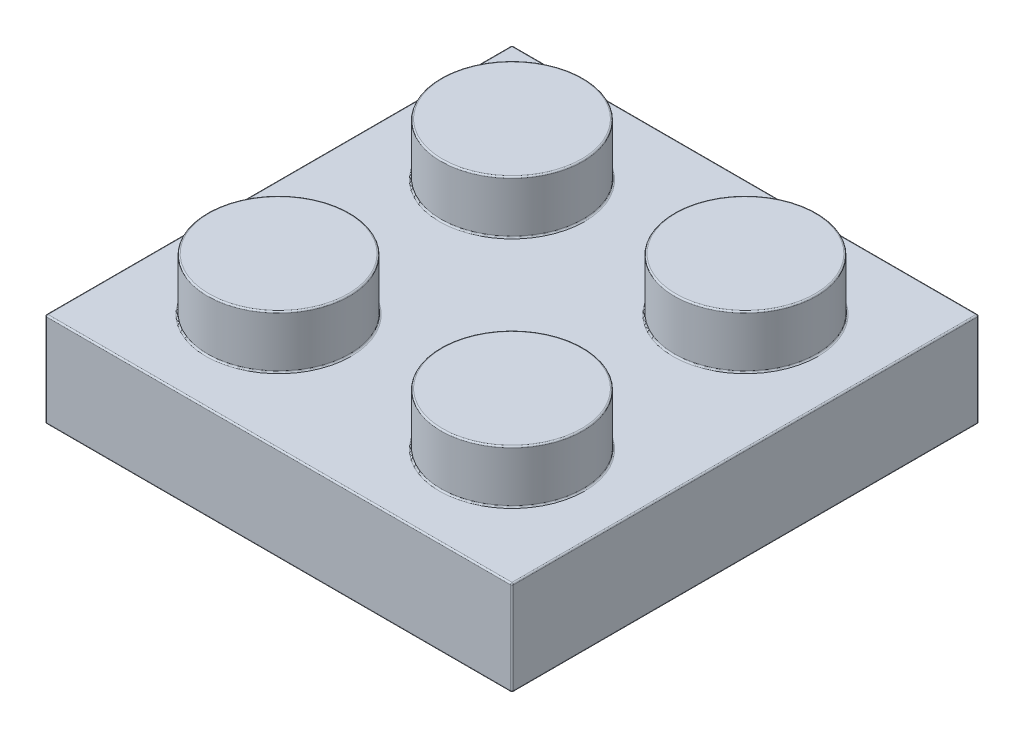
SolidWorks part; units mm, degrees
ref_plane "Front Plane" through (0, 0, 0) normal (0, 0, 1) x (1, 0, 0)
ref_plane "Top Plane" through (0, 0, 0) normal (0, 1, 0) x (1, 0, 0)
ref_plane "Right Plane" through (0, 0, 0) normal (1, 0, 0) x (0, 0, -1)
sketch "Sketch1" plane through (0, 0, 0) normal (0, 1, 0) x (1, 0, 0)
  line L1 (-3.98, 3.98) -> (3.98, 3.98)
  line L2 (-3.98, 3.98) -> (-3.98, -3.98)
  line L3 (-3.98, -3.98) -> (3.98, -3.98)
  line L4 (3.98, 3.98) -> (3.98, -3.98)
  line L5 (-3.98, 3.98) -> (3.98, -3.98) construction
  line L6 (-3.98, -3.98) -> (3.98, 3.98) construction
  point P0 (0, 0)
  dimension "D1" = 7.96
extrude "Extrude1" add sketch "Sketch1" along normal blind 3.22
sketch "Sketch2" plane through (0, 3.22, 0) normal (0, 1, 0) x (1, 0, 0)
  circle A0 centre (0, 0) radius 2.425
  dimension "D1" = 4.85
extrude "Extrude2" add sketch "Sketch2" along normal blind 1.8
pattern_linear "LPattern1" count 2 spacing 7.96 along (1, 0, 0) of "Extrude2", "Extrude1"
pattern_linear "LPattern2" count 2 spacing 7.96 along (0, 0, -1) of "LPattern1", "Extrude1", "Extrude2"
shell "Shell1" thickness 1.55
sketch "Sketch3" plane through (0, 1.67, 0) normal (0, -1, 0) x (1, 0, 0)
  line L0 (10.39, -10.39) -> (-2.43, -10.39) construction
  line L1 (-2.43, -10.39) -> (-2.43, 2.43) construction
  line L2 (-2.43, 2.43) -> (10.39, 2.43) construction
  line L3 (10.39, 2.43) -> (10.39, -10.39) construction
  line L4 (10.39, -10.39) -> (-2.43, -10.39)
  line L5 (-2.43, -10.39) -> (-2.43, 2.43)
  line L6 (-2.43, 2.43) -> (10.39, 2.43)
  line L7 (10.39, 2.43) -> (10.39, -10.39)
extrude "Extrude3" cut sketch "Sketch3" against normal blind 0.14
sketch "Sketch4" plane through (0, 1.81, 0) normal (0, -1, 0) x (1, 0, 0)
  line L0 (-2.43, -3.98) -> (10.39, -3.98) construction
  line L1 (-2.43, -10.39) -> (-2.43, 2.43) construction
  line L2 (10.39, 2.43) -> (10.39, -10.39) construction
  line L3 (3.98, 2.43) -> (3.98, -10.39) construction
  line L4 (-2.43, 2.43) -> (10.39, 2.43) construction
  line L5 (10.39, -10.39) -> (-2.43, -10.39) construction
  circle A0 centre (3.98, -3.98) radius 3.23
  circle A1 centre (3.98, -3.98) radius 2.37
  dimension "D1" = 6.46
  dimension "D2" = 0.86
extrude "Extrude4" add sketch "Sketch4" along normal up to surface (1.81 mm away) up to face at (3.98, 0, -3.98)
fillet "Fillet1" radius 0.05 44 edges at (-3.98, 3.22, -3.98) (3.98, 3.22, 3.98) (0, 3.22, 2.425) (0, 5.02, 2.425) (11.94, 0, -3.98) (11.94, 1.61, 3.98) (11.94, 3.22, -3.98) (7.96, 3.22, 2.425) (7.96, 5.02, 2.425) (3.98, 0, -11.94) (11.94, 1.61, -11.94) (-3.98, 1.61, -11.94) (3.98, 3.22, -11.94) (3.98, 0, 3.98) (0, 3.22, -5.535) (0, 5.02, -5.535) (7.96, 3.22, -5.535) (7.96, 5.02, -5.535) (-3.98, 0, -3.98) (-2.43, 0, -3.98) (-2.43, 0.905, -10.39) (3.98, 0, 2.43) (-2.43, 0.905, 2.43) (0, 3.47, 0.875) (10.39, 0, -3.98) (10.39, 0.905, 2.43) (7.96, 3.47, 0.875) (3.98, 0, -10.39) (10.39, 0.905, -10.39) (0, 3.47, -7.085) (7.96, 3.47, -7.085) (0, 1.81, 0.875) (7.96, 1.81, 0.875) (0, 1.81, -7.085) (7.96, 1.81, -7.085) (10.39, 1.81, -3.98) (3.98, 1.81, -10.39) (-3.98, 1.61, 3.98) (-2.43, 1.81, -3.98) (3.98, 1.81, 2.43) (3.98, 1.81, -0.75) (3.98, 1.81, -6.35) (3.98, 0, -0.75) (3.98, 0, -1.61)
